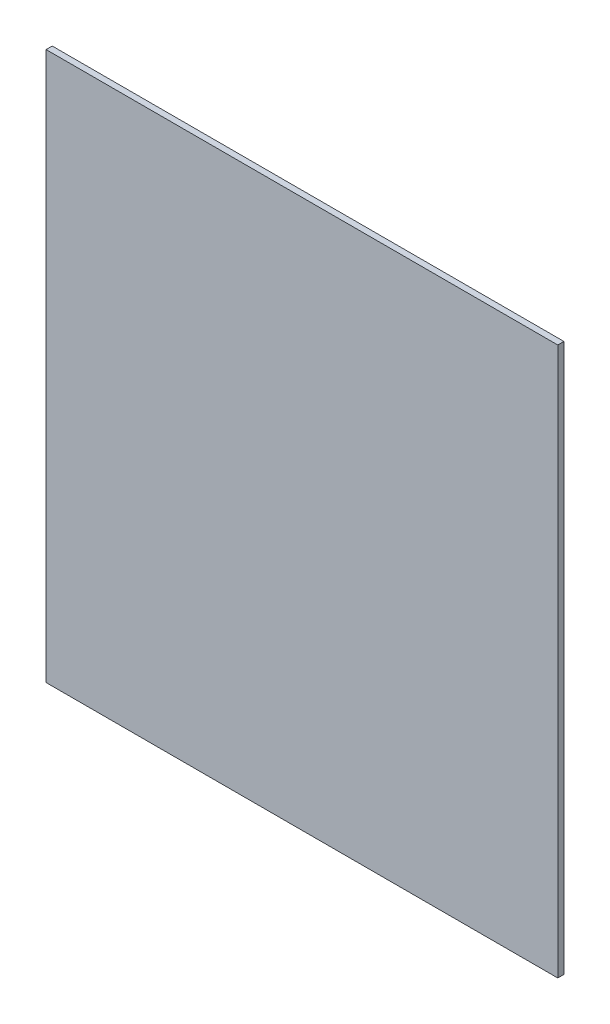
SolidWorks part; units mm, degrees
ref_plane "Front Plane" through (0, 0, 0) normal (0, 0, 1) x (1, 0, 0)
ref_plane "Top Plane" through (0, 0, 0) normal (0, 1, 0) x (1, 0, 0)
ref_plane "Right Plane" through (0, 0, 0) normal (1, 0, 0) x (0, 0, -1)
sketch "Sketch1" plane through (0, 0, 0) normal (0, 0, 1) x (1, 0, 0)
  line L0 (62.1, -267.4) -> (-0.4, -267.4) construction
  line L1 (0, 0) -> (249.6, 0)
  line L2 (0, 0) -> (0, -267.4)
  line L3 (0, -267.4) -> (249.6, -267.4)
  line L4 (249.6, 0) -> (249.6, -267.4)
  dimension "D2" = 249.6
extrude "Boss-Extrude1" add sketch "Sketch1" along normal blind 3
